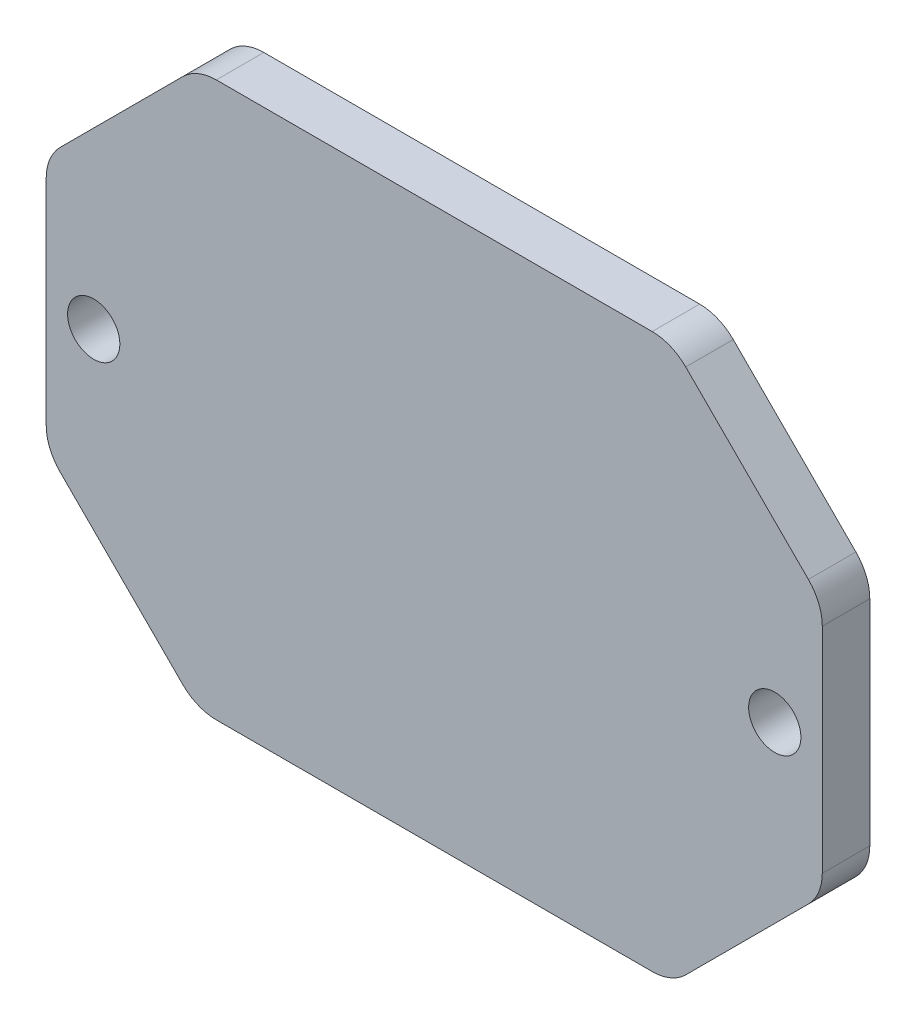
SolidWorks part; units mm, degrees
material "ABS"
ref_plane "前视基准面" through (0, 0, 0) normal (0, 0, 1) x (1, 0, 0)
ref_plane "上视基准面" through (0, 0, 0) normal (0, 1, 0) x (1, 0, 0)
ref_plane "右视基准面" through (0, 0, 0) normal (1, 0, 0) x (0, 0, -1)
sketch "草图1" plane through (0, 0, 0) normal (0, 0, 1) x (1, 0, 0)
  line L1 (-24.5, 17.4981) -> (24.5, 17.4981)
  line L2 (-24.5, 17.4981) -> (-24.5, -17.4981)
  line L3 (-24.5, -17.4981) -> (24.5, -17.4981)
  line L4 (24.5, 17.4981) -> (24.5, -17.4981)
  line L5 (-24.5, 17.4981) -> (24.5, -17.4981) construction
  line L6 (-24.5, -17.4981) -> (24.5, 17.4981) construction
  point P0 (0, 0)
  dimension "D1" = 49
  dimension "D2" = 34.9962
extrude "凸台-拉伸1" add sketch "草图1" along normal blind 3
chamfer "倒角1" distance 9.5 angle 45 4 edges at (-24.5, 17.4981, 1.5) (-24.5, -17.4981, 1.5) (24.5, -17.4981, 1.5) (24.5, 17.4981, 1.5)
fillet "圆角1" radius 3 8 edges at (-24.5, -7.9981, 1.5) (-15, -17.4981, 1.5) (15, -17.4981, 1.5) (24.5, -7.9981, 1.5) (24.5, 7.9981, 1.5) (15, 17.4981, 1.5) (-15, 17.4981, 1.5) (-24.5, 7.9981, 1.5)
sketch "草图2" plane through (0, 0, 3) normal (0, 0, 1) x (1, 0, 0)
  line L0 (-21.5, 0) -> (21.5, 0) construction
  line L1 (24.5, -6.7555) -> (24.5, 6.7555) construction
  line L2 (-24.5, 6.7555) -> (-24.5, -6.7555) construction
  circle A0 centre (-21.5, 0) radius 1.65
  circle A1 centre (21.5, 0) radius 1.65
  dimension "D3" = 3.3
  dimension "D1" = 3
  dimension "D2" = 3
extrude "切除-拉伸1" cut sketch "草图2" against normal through all
